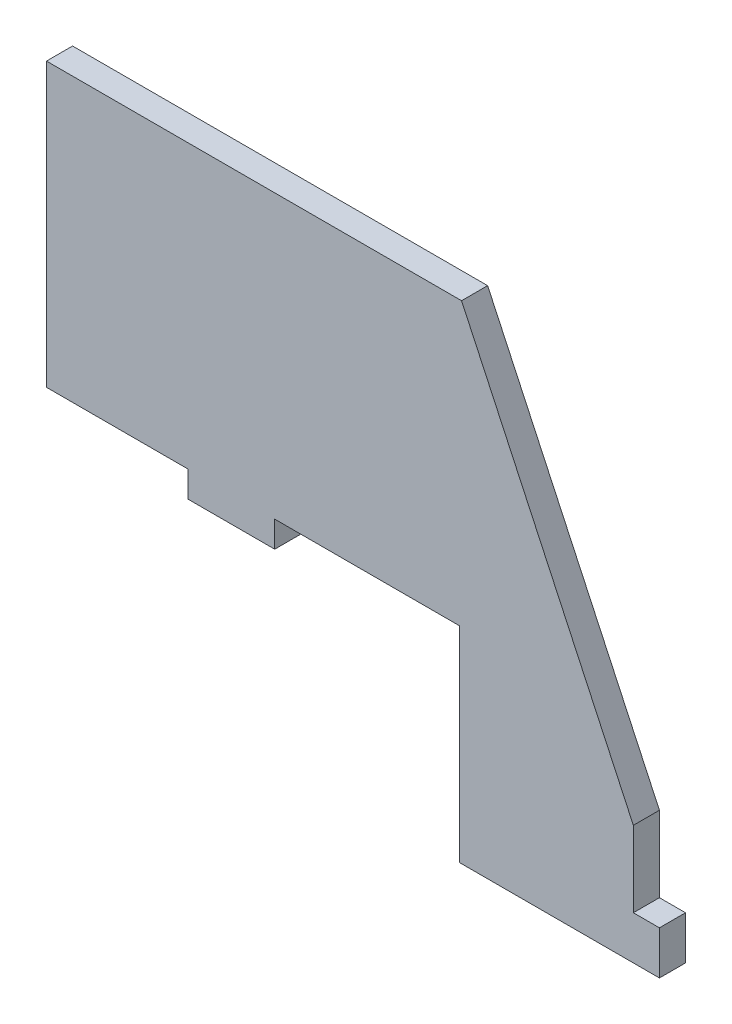
SolidWorks part; units mm, degrees
ref_plane "Plan de face" through (0, 0, 0) normal (0, 0, 1) x (1, 0, 0)
ref_plane "Plan de dessus" through (0, 0, 0) normal (0, 1, 0) x (1, 0, 0)
ref_plane "Plan de droite" through (0, 0, 0) normal (1, 0, 0) x (0, 0, -1)
sketch "Esquisse1" plane through (0, 0, 0) normal (0, 0, 1) x (1, 0, 0)
  line L1 (-67.5, 56.085) -> (67.5, 56.085)
  line L2 (-67.5, 56.085) -> (-67.5, -56.085)
  line L3 (-67.5, -56.085) -> (67.5, -56.085)
  line L4 (67.5, 56.085) -> (67.5, -56.085)
  dimension "D1" = 135
  dimension "D2" = 112.17
  dimension "D3" = 67.5
  dimension "D4" = 56.085
extrude "Boss.-Extru.1" add sketch "Esquisse1" along normal blind 6
sketch "Esquisse2" plane through (0, 0, 6) normal (0, 0, 1) x (1, 0, 0)
  line L0 (-67.5, -56.085) -> (67.5, -56.085) construction
  line L1 (27.5, -56.085) -> (-67.5, -56.085)
  line L2 (27.5, -56.085) -> (27.5, -8.915)
  line L3 (-38.5, -8.915) -> (27.5, -8.915)
  line L4 (-67.5, -56.085) -> (-67.5, -8.915)
  line L5 (-67.5, 56.085) -> (-67.5, -56.085) construction
  line L7 (67.5, -28.665) -> (27.9804, 56.085)
  line L8 (-38.5, -8.915) -> (-67.5, -8.915)
  line L9 (67.5, -56.085) -> (67.5, 56.085) construction
  line L10 (67.5, 56.085) -> (-67.5, 56.085) construction
  line L11 (27.9804, 56.085) -> (67.5, 56.085)
  line L12 (67.5, 56.085) -> (67.5, -28.665)
  dimension "D1" = 47.17
  dimension "D2" = 95
  dimension "D3" = 27.42
  dimension "D4" = 155
  dimension "D5" = 115
extrude "Enlèv. mat.-Extru.1" cut sketch "Esquisse2" against normal blind 6
sketch "Esquisse3" plane through (0, 0, 6) normal (0, 0, 1) x (1, 0, 0)
  line L0 (67.5, -56.085) -> (67.5, -28.665) construction
  line L1 (67.5, -56.085) -> (73.5, -56.085)
  line L2 (67.5, -56.085) -> (67.5, -46.085)
  line L3 (67.5, -46.085) -> (73.5, -46.085)
  line L4 (73.5, -56.085) -> (73.5, -46.085)
  line L6 (-35, -8.915) -> (-15, -8.915)
  line L7 (-35, -8.915) -> (-35, -14.915)
  line L8 (-35, -14.915) -> (-15, -14.915)
  line L9 (-15, -8.915) -> (-15, -14.915)
  line L10 (27.5, -8.915) -> (-67.5, -8.915) construction
  line L16 (27.5, -56.085) -> (27.5, -8.915) construction
  dimension "D3" = 6
  dimension "D4" = 20
  dimension "D5" = 42.5
  dimension "D6" = 10
  dimension "D7" = 6
extrude "Boss.-Extru.2" add sketch "Esquisse3" against normal blind 6
equation "\"D3@Esquisse1\"=\"D1@Esquisse1\"/2"
equation "\"D4@Esquisse1\"=\"D2@Esquisse1\"/2"
